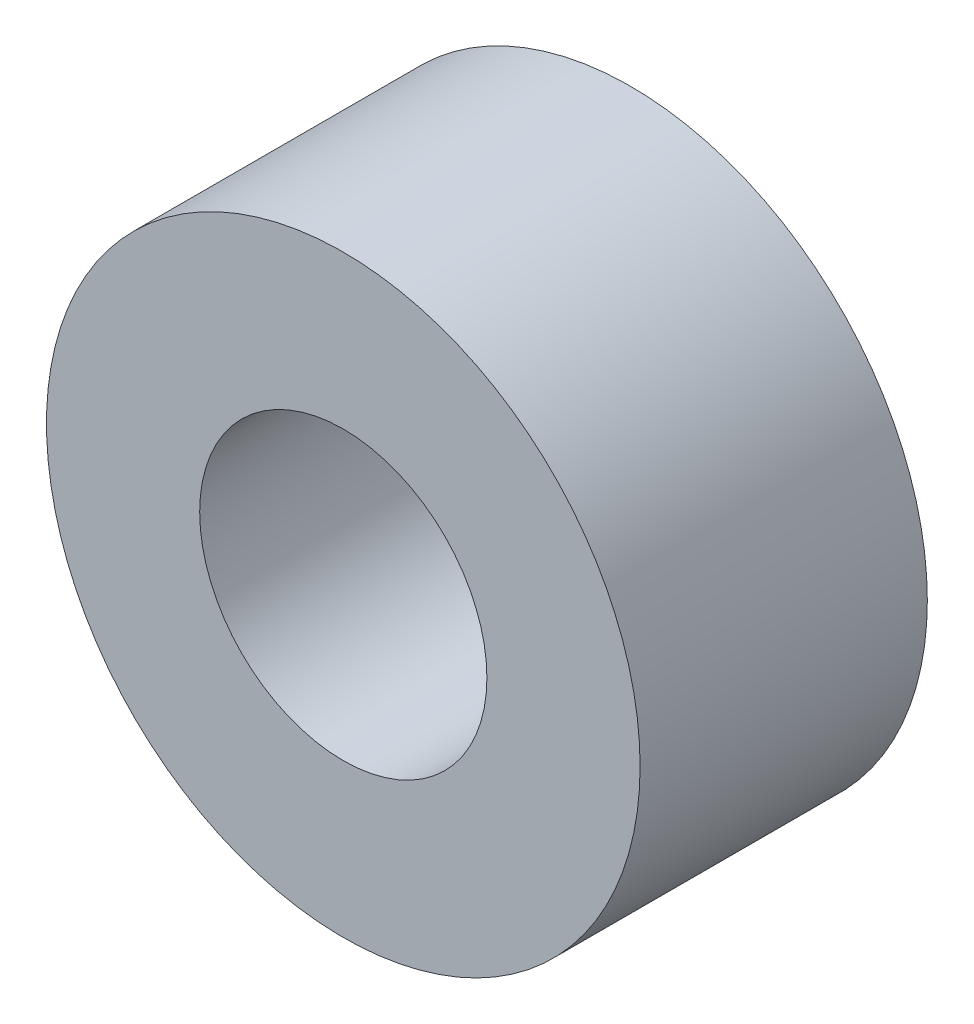
SolidWorks part; units mm, degrees
ref_plane "Front Plane" through (0, 0, 0) normal (0, 0, 1) x (1, 0, 0)
ref_plane "Top Plane" through (0, 0, 0) normal (0, 1, 0) x (1, 0, 0)
ref_plane "Right Plane" through (0, 0, 0) normal (1, 0, 0) x (0, 0, -1)
sketch "Sketch1" plane through (0, 0, 0) normal (0, 0, 1) x (1, 0, 0)
  circle A0 centre (0, 0) radius 3.1
  circle A1 centre (0, 0) radius 1.425
  dimension "D1" = 6.2
  dimension "D2" = 2.85
extrude "Boss-Extrude4" [suppressed] add sketch "Sketch1" along normal blind 9
sketch "Sketch2" plane through (0, 0, 0) normal (0, 0, 1) x (1, 0, 0)
  circle A0 centre (0, 0) radius 3.1
  circle A1 centre (0, 0) radius 1.5
  dimension "D1" = 6.2
  dimension "D2" = 3
extrude "Boss-Extrude5" add sketch "Sketch2" along normal blind 3
sketch "Sketch3" plane through (0, 0, 0) normal (0, 0, 1) x (1, 0, 0)
  circle A0 centre (0, 0) radius 3.1
  circle A1 centre (0, 0) radius 2.1
  dimension "D1" = 6.2
  dimension "D2" = 4.2
extrude "Boss-Extrude6" [suppressed] add sketch "Sketch3" along normal blind 5
